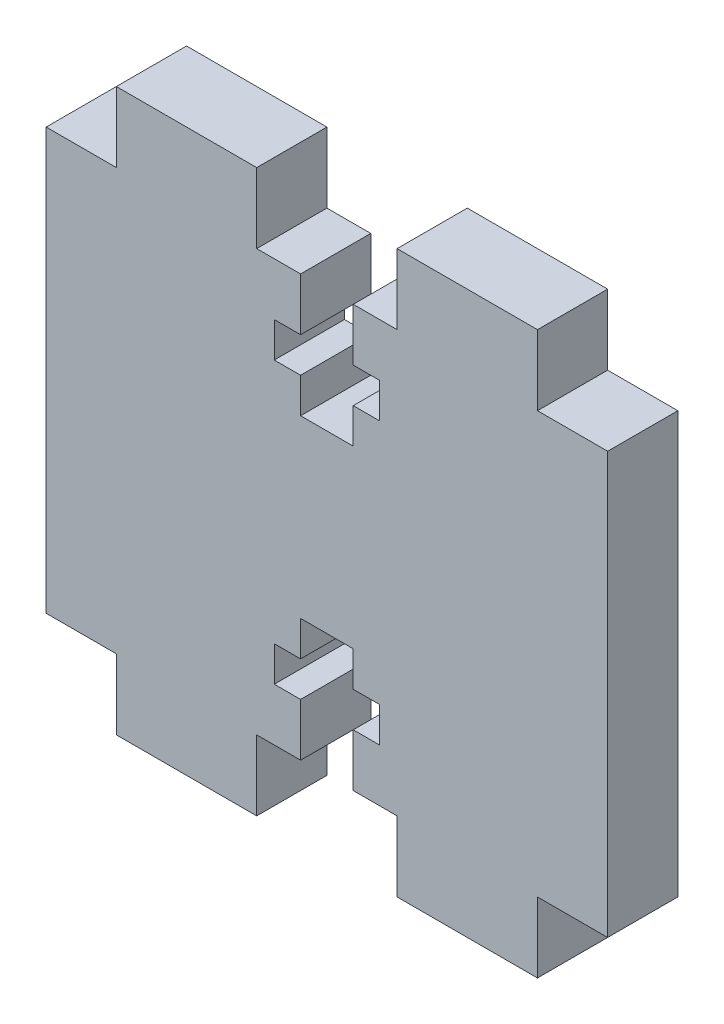
SolidWorks part; units mm, degrees
ref_plane "Front Plane" through (0, 0, 0) normal (0, 0, 1) x (1, 0, 0)
ref_plane "Top Plane" through (0, 0, 0) normal (0, 1, 0) x (1, 0, 0)
ref_plane "Right Plane" through (0, 0, 0) normal (1, 0, 0) x (0, 0, -1)
sketch "Sketch1" plane through (0, 0, 0) normal (0, 0, 1) x (1, 0, 0)
  line L0 (27.7812, 44.45) -> (31.75, 44.45)
  line L1 (6.35, 0) -> (19.05, 0)
  line L2 (0, 6.35) -> (0, 44.45)
  line L3 (6.35, 50.8) -> (19.05, 50.8)
  line L4 (50.8, 6.35) -> (50.8, 44.45)
  line L5 (0, 44.45) -> (6.35, 44.45)
  line L8 (6.35, 44.45) -> (6.35, 50.8)
  line L10 (19.05, 50.8) -> (19.05, 44.45)
  line L11 (19.05, 44.45) -> (23.0187, 44.45)
  line L12 (31.75, 50.8) -> (31.75, 44.45)
  line L14 (44.45, 50.8) -> (44.45, 44.45)
  line L15 (44.45, 44.45) -> (50.8, 44.45)
  line L17 (27.7812, 17.4625) -> (27.7812, 14.2875)
  line L18 (27.7812, 33.3375) -> (23.0187, 33.3375)
  line L19 (23.0187, 33.3375) -> (23.0187, 36.5125)
  line L20 (23.0187, 36.5125) -> (20.6375, 36.5125)
  line L21 (20.6375, 36.5125) -> (20.6375, 39.6875)
  line L22 (20.6375, 39.6875) -> (23.0187, 39.6875)
  line L23 (23.0187, 39.6875) -> (23.0187, 44.45)
  line L24 (27.7812, 39.6875) -> (27.7812, 44.45)
  line L25 (30.1625, 39.6875) -> (27.7812, 39.6875)
  line L26 (30.1625, 36.5125) -> (30.1625, 39.6875)
  line L27 (27.7812, 36.5125) -> (30.1625, 36.5125)
  line L28 (27.7812, 33.3375) -> (27.7812, 36.5125)
  line L29 (27.7812, 14.2875) -> (30.1625, 14.2875)
  line L30 (30.1625, 14.2875) -> (30.1625, 11.1125)
  line L31 (30.1625, 11.1125) -> (27.7813, 11.1125)
  line L32 (27.7813, 11.1125) -> (27.7813, 6.35)
  line L33 (23.0188, 11.1125) -> (23.0188, 6.35)
  line L34 (20.6375, 11.1125) -> (23.0188, 11.1125)
  line L35 (20.6375, 14.2875) -> (20.6375, 11.1125)
  line L36 (23.0187, 14.2875) -> (20.6375, 14.2875)
  line L37 (23.0187, 17.4625) -> (23.0187, 14.2875)
  line L38 (27.7812, 17.4625) -> (23.0187, 17.4625)
  line L40 (44.45, 6.35) -> (50.8, 6.35)
  line L41 (44.45, 0) -> (44.45, 6.35)
  line L43 (31.75, 0) -> (31.75, 6.35)
  line L44 (19.05, 6.35) -> (23.0188, 6.35)
  line L45 (19.05, 0) -> (19.05, 6.35)
  line L47 (6.35, 6.35) -> (6.35, 0)
  line L50 (0, 6.35) -> (6.35, 6.35)
  line L52 (31.75, 50.8) -> (44.45, 50.8)
  line L53 (31.75, 0) -> (44.45, 0)
  line L55 (27.7813, 6.35) -> (31.75, 6.35)
  dimension "D3" = 6.35
  dimension "D4" = 12.7
  dimension "D5" = 12.7
  dimension "D6" = 12.7
  dimension "D7" = 6.35
  dimension "D8" = 6.35
  dimension "D9" = 6.35
  dimension "D11" = 2.3813
  dimension "D12" = 4.7625
  dimension "D13" = 3.175
  dimension "D14" = 3.175
extrude "Boss-Extrude1" add sketch "Sketch1" along normal blind 6.35
